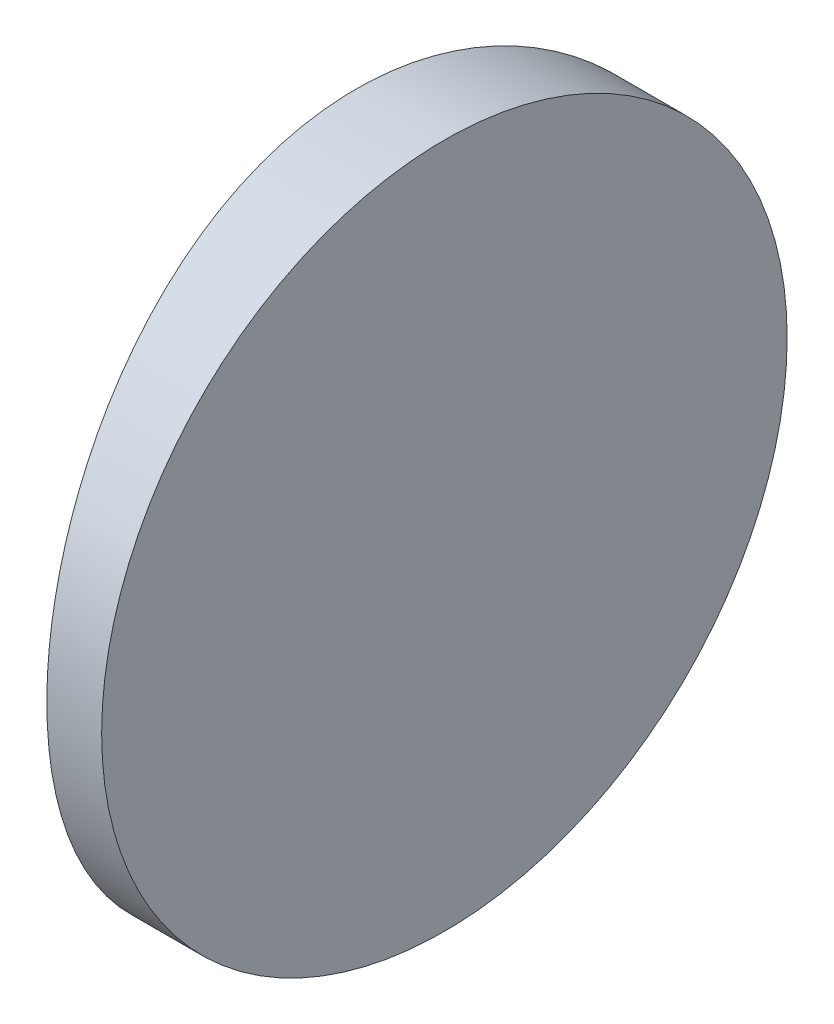
SolidWorks part; units mm, degrees
ref_plane "前视基准面" through (0, 0, 0) normal (0, 0, 1) x (1, 0, 0)
ref_plane "上视基准面" through (0, 0, 0) normal (0, 1, 0) x (1, 0, 0)
ref_plane "右视基准面" through (0, 0, 0) normal (1, 0, 0) x (0, 0, -1)
sketch "草图1" plane through (0, 0, 0) normal (0, 1, 0) x (1, 0, 0)
  line L0 (10.7432, 0) -> (-75.2096, 0) construction
  line L1 (-59.0239, 12.5) -> (-57.0248, 12.5)
  line L2 (-59.0239, -12.5) -> (-57.0248, -12.5)
  line L3 (-57.0248, 12.5) -> (-57.0248, -12.5)
  arc A0 (-59.0239, 12.5) -> (-59.0239, -12.5) centre (4.3552, 0) ccw
  point P2 (-75.2096, 0)
  point P19 (-60.2448, 0)
  point P20 (-57.0248, 0)
  dimension "D2" = 12.5
  dimension "D3" = 64.6
  dimension "D4" = 3.22
  dimension "D1" = 12.5
extrude "凸台-拉伸1" add sketch "草图1" along normal blind 25 contours A0 L2 L3 L1
sketch "草图2" plane through (-57.0248, 0, 0) normal (1, 0, 0) x (0, 0, -1)
  line L0 (12.5, 0) -> (-12.5, 0) construction
  line L7 (-12.5, 0) -> (12.5, 0)
  line L8 (12.5, 0) -> (12.5, 25)
  line L9 (12.5, 25) -> (-12.5, 25)
  line L10 (-12.5, 25) -> (-12.5, 0)
  line L11 (-12.5, 0) -> (12.5, 0)
  line L12 (12.5, 0) -> (12.5, 25)
  line L13 (12.5, 25) -> (-12.5, 25)
  line L14 (-12.5, 25) -> (-12.5, 0)
  circle A0 centre (0, 12.5) radius 12.5
  line M1 (-12.5, 0) -> (12.5, 0)
  line M2 (12.5, 0) -> (12.5, 25)
  line M3 (12.5, 25) -> (-12.5, 25)
  line M4 (-12.5, 25) -> (-12.5, 0)
  dimension "D1" = 25
  dimension "D4" = 12.5
  dimension "D2" = 12.5
  dimension "D3" = 0
extrude "切除-拉伸8" cut sketch "草图2" against normal blind 12.7 contours A0 L13 M4 | A0 L12 M3 | A0 L11 M2 | A0 L14 M1
